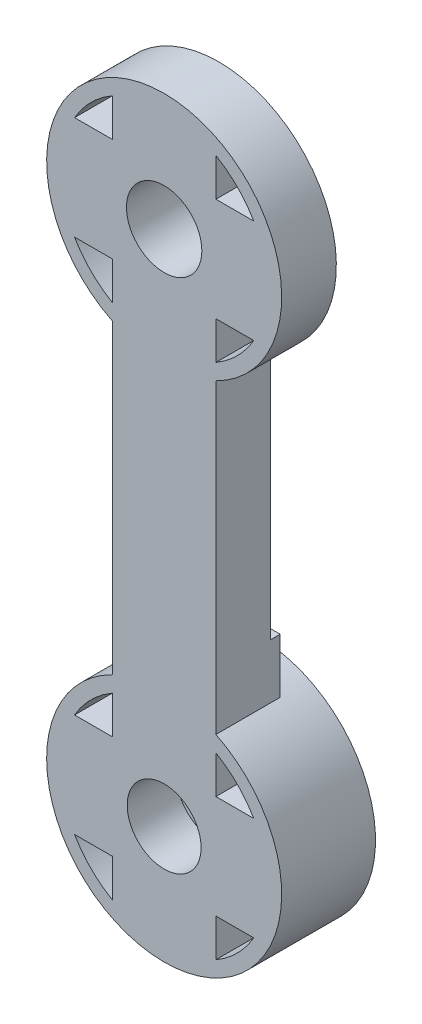
SolidWorks part; units mm, degrees
ref_plane "Front Plane" through (0, 0, 0) normal (0, 0, 1) x (1, 0, 0)
ref_plane "Top Plane" through (0, 0, 0) normal (0, 1, 0) x (1, 0, 0)
ref_plane "Right Plane" through (0, 0, 0) normal (1, 0, 0) x (0, 0, -1)
sketch "Sketch1" plane through (0, 0, 0) normal (0, 0, 1) x (1, 0, 0)
  line L5 (0, -17.5) -> (12.7696, -17.5) construction
  line L26 (0, 0) -> (0, -35) construction
  line L32 (0, 3.5) -> (7.1381, 3.5)
  line L33 (7.1381, 3.5) -> (-7.1381, 3.5)
  line L34 (0, -3.5) -> (7.1381, -3.5)
  line L35 (7.1381, -3.5) -> (-7.1381, -3.5)
  line L36 (3.5, -35) -> (3.5, -41.0622)
  line L37 (-3.5, -35) -> (-3.5, -41.0622)
  line L38 (-3.5, 0) -> (-3.5, 6.0622)
  line L45 (-3.5, 0) -> (-3.5, -35)
  line L47 (3.5, 0) -> (3.5, -35)
  line L48 (3.5, 0) -> (3.5, 6.0622)
  line L49 (7.1381, -31.5) -> (-7.1381, -31.5)
  line L50 (0, -31.5) -> (7.1381, -31.5)
  line L51 (7.1381, -38.5) -> (-7.1381, -38.5)
  line L52 (0, -38.5) -> (7.1381, -38.5)
  circle A0 centre (0, 0) radius 7.95
  circle A1 centre (0, 0) radius 3.5
  circle A2 centre (0, 0) radius 7
  circle A6 centre (0, 0) radius 1.5
  circle A11 centre (0, -35) radius 1.5
  circle A12 centre (0, -35) radius 7
  circle A13 centre (0, -35) radius 3.5
  circle A14 centre (0, -35) radius 7.95
  point P20 (0, -35)
  point P34 (0, -35)
  point P42 (0, 0)
  dimension "D1" = 15.9
  dimension "D2" = 7
  dimension "D6" = 14
  dimension "D9" = 3
  dimension "D3" = 7
  dimension "D7" = 35
extrude "Boss-Extrude4" add sketch "Sketch1" along normal blind 3 contours L48 A2 L38 L33 L32 | A2 L32 A0 L33 | L45 A14 L47 A0 | A14 L51 A12 | A12 L36 L51 L37 | A14 L49 A12 L51 | L36 A13 L51 | L51 A13 L37 | A14 L51 A12 L49 | A13 A11 | L45 A13 L49 | L49 A13 L47 | A12 L45 L49 L47 | A14 L49 A12 L45 | A14 L47 A12 L49 | A14 L45 A12 L47 | A12 L51 L37 L45 L49 | A12 L50 L47 L36 L52 | L45 A2 L47 L34 L35 | A2 L45 A0 L47 | A2 L47 A0 L34 | A2 L34 A0 L32 | A2 L33 A0 L35 | A2 L35 A0 L45 | L33 A2 L35 L45 L38 | L35 A2 L33 L48 L47 | A1 L34 L47 | A1 A6 | A1 L45 L35 | A1 L33 L38 | A1 L48 L32
sketch "Sketch3" plane through (0, 0, 0) normal (0, 0, -1) x (-1, 0, 0)
  line L0 (-3.5, 6.0622) -> (-3.5, 3.5)
  line L1 (-3.5, 3.5) -> (-6.0622, 3.5)
  line L2 (-3.5, -6.0622) -> (-3.5, -3.5)
  line L3 (-3.5, -3.5) -> (-6.0622, -3.5)
  line L4 (3.5, -6.0622) -> (3.5, -3.5)
  line L5 (3.5, -3.5) -> (6.0622, -3.5)
  line L6 (3.5, 6.0622) -> (3.5, 3.5)
  line L7 (3.5, 3.5) -> (6.0622, 3.5)
  line L8 (0, 0) -> (0, -35) construction
  line L9 (0, -35) -> (0, -17.5) construction
  line L10 (0, -17.5) -> (14.5774, -17.5) construction
  line L11 (-3.5, 3.5) -> (-6.0622, 3.5)
  line L12 (-3.5, 6.0622) -> (-3.5, 3.5)
  line L13 (-3.5, -3.5) -> (-6.0622, -3.5)
  line L14 (-3.5, -6.0622) -> (-3.5, -3.5)
  line L15 (3.5, -3.5) -> (6.0622, -3.5)
  line L16 (3.5, -6.0622) -> (3.5, -3.5)
  line L17 (3.5, 3.5) -> (6.0622, 3.5)
  line L18 (3.5, 6.0622) -> (3.5, 3.5)
  line L19 (3.5, -41.0622) -> (3.5, -38.5)
  line L20 (3.5, -38.5) -> (6.0622, -38.5)
  line L21 (3.5, -28.9378) -> (3.5, -31.5)
  line L22 (3.5, -31.5) -> (6.0622, -31.5)
  line L23 (-3.5, -28.9378) -> (-3.5, -31.5)
  line L24 (-3.5, -31.5) -> (-6.0622, -31.5)
  line L25 (-3.5, -41.0622) -> (-3.5, -38.5)
  line L26 (-3.5, -38.5) -> (-6.0622, -38.5)
  line L27 (3.5, -38.5) -> (6.0622, -38.5)
  line L28 (3.5, -41.0622) -> (3.5, -38.5)
  line L29 (3.5, -31.5) -> (6.0622, -31.5)
  line L30 (3.5, -28.9378) -> (3.5, -31.5)
  line L31 (-3.5, -31.5) -> (-6.0622, -31.5)
  line L32 (-3.5, -28.9378) -> (-3.5, -31.5)
  line L33 (-3.5, -38.5) -> (-6.0622, -38.5)
  line L34 (-3.5, -41.0622) -> (-3.5, -38.5)
  circle A0 centre (0, 0) radius 1.5
  circle A1 centre (0, 0) radius 7.95
  circle A2 centre (0, 0) radius 7
  circle A3 centre (0, -35) radius 7
  circle A4 centre (0, -35) radius 7.95
  circle A5 centre (0, -35) radius 1.5
  line M2 (3.5, -38.5) -> (6.0622, -38.5)
  arc M3 (6.0622, -38.5) -> (3.5, -41.0622) centre (0, -35) cw
  line M4 (3.5, -41.0622) -> (3.5, -38.5)
  line M5 (-3.5, -38.5) -> (-3.5, -41.0622)
  arc M6 (-3.5, -41.0622) -> (-6.0622, -38.5) centre (0, -35) cw
  line M7 (-6.0622, -38.5) -> (-3.5, -38.5)
  arc M9 (3.5, -7.1381) -> (-3.5, -7.1381) centre (0, 0) ccw
  arc M11 (-3.5, -27.8619) -> (3.5, -27.8619) centre (0, -35) ccw
  line M12 (6.0622, -31.5) -> (3.5, -31.5)
  line M13 (3.5, -31.5) -> (3.5, -28.9378)
  arc M14 (3.5, -28.9378) -> (6.0622, -31.5) centre (0, -35) cw
  arc M15 (-3.5, -6.0622) -> (-6.0622, -3.5) centre (0, 0) cw
  line M16 (-6.0622, -3.5) -> (-3.5, -3.5)
  line M17 (-3.5, -3.5) -> (-3.5, -6.0622)
  line M18 (-3.5, -31.5) -> (-6.0622, -31.5)
  arc M19 (-6.0622, -31.5) -> (-3.5, -28.9378) centre (0, -35) cw
  line M20 (-3.5, -28.9378) -> (-3.5, -31.5)
  line M21 (3.5, -3.5) -> (6.0622, -3.5)
  arc M22 (6.0622, -3.5) -> (3.5, -6.0622) centre (0, 0) cw
  line M23 (3.5, -6.0622) -> (3.5, -3.5)
  line M24 (6.0622, 3.5) -> (3.5, 3.5)
  line M25 (3.5, 3.5) -> (3.5, 6.0622)
  arc M26 (3.5, 6.0622) -> (6.0622, 3.5) centre (0, 0) cw
  arc M27 (-6.0622, 3.5) -> (-3.5, 6.0622) centre (0, 0) cw
  line M28 (-3.5, 6.0622) -> (-3.5, 3.5)
  line M29 (-3.5, 3.5) -> (-6.0622, 3.5)
  circle M30 centre (0, 0) radius 1.5
  circle M31 centre (0, -35) radius 1.5
  dimension "D1" = 15.9
extrude "Boss-Extrude5" add sketch "Sketch3" along normal blind 3 contours A1 A2 M9 M26 M22 M15 M27 | A2 M25 M28 M29 M16 M17 M23 M21 M24 M30 | A3 M4 M2 M12 M13 M20 M18 M7 M5 M31 | A4 A3 M11 M3 M6 M19 M14
sketch "Sketch4" plane through (0, 0, 3) normal (0, 0, 1) x (1, 0, 0)
  line L0 (0, 0) -> (0, -35) construction
  line L1 (0, -35) -> (0, 0) construction
  line L2 (0, -17.5) -> (19.6941, -17.5) construction
  circle A1 centre (0, -35) radius 2.5
  circle A2 centre (0, 0) radius 2.5
  dimension "D2" = 5
extrude "Cut-Extrude1" cut sketch "Sketch4" against normal blind 1.5
sketch "Sketch5" plane through (0, 0, -3) normal (0, 0, -1) x (-1, 0, 0)
  circle A0 centre (0, 0) radius 7
extrude "Cut-Extrude2" cut sketch "Sketch5" against normal blind 2
sketch "Sketch6" plane through (0, 0, -3) normal (0, 0, -1) x (-1, 0, 0)
  circle A0 centre (0, -35) radius 7.95
extrude "Cut-Extrude3" cut sketch "Sketch6" against normal blind 1
sketch "Sketch7" plane through (0, 0, 1.5) normal (0, 0, 1) x (1, 0, 0)
  circle A0 centre (0, -35) radius 2.5
extrude "Cut-Extrude4" cut sketch "Sketch7" against normal blind 1.85
sketch "Sketch8" plane through (0, 0, -3) normal (0, 0, -1) x (-1, 0, 0)
  circle A0 centre (0, 0) radius 7.95
  circle A1 centre (0, 0) radius 7
extrude "Boss-Extrude6" add sketch "Sketch8" along normal blind 0.7
sketch "Sketch9" plane through (0, 0, -2) normal (0, 0, -1) x (-1, 0, 0)
  line L0 (-3.5, -28.9378) -> (-3.5, -31.5)
  line L1 (-3.5, -31.5) -> (-6.0622, -31.5)
  line L2 (-6.0622, -38.5) -> (-3.5, -38.5)
  line L3 (-3.5, -38.5) -> (-3.5, -41.0622)
  line L4 (6.0622, -38.5) -> (3.5, -38.5)
  line L5 (3.5, -38.5) -> (3.5, -41.0622)
  line L6 (3.5, -28.9378) -> (3.5, -31.5)
  line L7 (3.5, -31.5) -> (6.0622, -31.5)
  circle A0 centre (0, -35) radius 7.95
  circle A1 centre (0, -35) radius 7
  circle A2 centre (0, -35) radius 1.5
  line M1 (6.0622, -31.5) -> (3.5, -31.5)
  line M2 (3.5, -31.5) -> (3.5, -28.9378)
  arc M3 (3.5, -28.9378) -> (6.0622, -31.5) centre (0, -35) cw
  arc M4 (-3.5, -41.0622) -> (-6.0622, -38.5) centre (0, -35) cw
  line M5 (-6.0622, -38.5) -> (-3.5, -38.5)
  line M6 (-3.5, -38.5) -> (-3.5, -41.0622)
  arc M7 (6.0622, -38.5) -> (3.5, -41.0622) centre (0, -35) cw
  line M8 (3.5, -41.0622) -> (3.5, -38.5)
  line M9 (3.5, -38.5) -> (6.0622, -38.5)
  circle M10 centre (0, -35) radius 7.95
  line M11 (-3.5, -31.5) -> (-6.0622, -31.5)
  arc M12 (-6.0622, -31.5) -> (-3.5, -28.9378) centre (0, -35) cw
  line M13 (-3.5, -28.9378) -> (-3.5, -31.5)
  circle M14 centre (0, -35) radius 1.5
extrude "Boss-Extrude8" add sketch "Sketch9" along normal blind 0.7 contours A1 M2 M13 M11 M5 M6 M8 M9 M1 M14 | A1 M10 M3 M7 M4 M12 | A0
sketch "Sketch10" plane through (0, 0, 0) normal (0, 0, -1) x (-1, 0, 0)
  line L2 (-3.5, -7.1381) -> (-3.5, -27.8619)
  line L4 (3.5, -7.1381) -> (3.5, -27.8619)
  circle A0 centre (0, 0) radius 7.95
  circle A1 centre (0, -35) radius 7.95
  line M1 (-3.5, -7.1381) -> (-3.5, -27.8619)
  arc M2 (-3.5, -27.8619) -> (3.5, -27.8619) centre (0, -35) cw
  line M3 (3.5, -27.8619) -> (3.5, -7.1381)
  arc M4 (3.5, -7.1381) -> (-3.5, -7.1381) centre (0, 0) cw
extrude "Boss-Extrude9" add sketch "Sketch10" along normal blind 0.7 contours M4 M1 M2 M3
sketch "Sketch11" plane through (3.5, 0, 0) normal (1, 0, 0) x (0, 0, -1)
  line L0 (-3, -42.95) -> (2.7, -42.95) construction
  line L1 (3.7, 7.95) -> (0.7, 7.95)
  line L2 (3.7, 7.95) -> (3.7, -7.95)
  line L3 (3.7, -7.95) -> (0.7, -7.95)
  line L4 (0.7, 7.95) -> (0.7, -7.95)
  line L5 (2.7, -27.05) -> (0.7, -27.05)
  line L6 (2.7, -27.05) -> (2.7, -42.95)
  line L7 (2.7, -42.95) -> (0.7, -42.95)
  line L8 (0.7, -27.05) -> (0.7, -42.95)
extrude "Cut-Extrude5" cut sketch "Sketch11" against normal through all both and the other way through all
sketch "Sketch12" plane through (0, 0, -0.7) normal (0, 0, -1) x (-1, 0, 0)
  line L0 (3.5, -27.8619) -> (3.5, -7.1381) construction
  line L1 (-3.5, -27.8619) -> (3.5, -27.8619)
  line L2 (-3.5, -27.8619) -> (-3.5, -24.1619)
  line L3 (-3.5, -24.1619) -> (3.5, -24.1619)
  line L4 (3.5, -27.8619) -> (3.5, -24.1619)
  circle A0 centre (0, -35) radius 7.95
  line M3 (3.5, -27.8619) -> (3.5, -7.1381)
  line M5 (-3.5, -7.1381) -> (-3.5, -27.8619)
  dimension "D1" = 3.7
extrude "Boss-Extrude10" add sketch "Sketch12" along normal blind 0.65 contours A0 L3 M3 M5
sketch "Sketch13" plane through (0, 0, -0.7) normal (0, 0, -1) x (-1, 0, 0)
  line L0 (-6.0622, -31.5) -> (-3.5, -31.5)
  line L1 (-3.5, -31.5) -> (-3.5, -28.9378)
  line L2 (3.5, -28.9378) -> (3.5, -31.5)
  line L3 (3.5, -31.5) -> (6.0622, -31.5)
  line L4 (-6.0622, -38.5) -> (-3.5, -38.5)
  line L5 (-3.5, -38.5) -> (-3.5, -41.0622)
  line L6 (6.0622, -38.5) -> (3.5, -38.5)
  line L7 (3.5, -38.5) -> (3.5, -41.0622)
  circle A0 centre (0, -35) radius 1.5
  circle A1 centre (0, -35) radius 7.95
  circle A2 centre (0, -35) radius 7
  arc M1 (-6.0622, -31.5) -> (-3.5, -28.9378) centre (0, -35) cw
  line M2 (-3.5, -28.9378) -> (-3.5, -31.5)
  line M3 (-3.5, -31.5) -> (-6.0622, -31.5)
  line M4 (3.5, -31.5) -> (3.5, -28.9378)
  arc M5 (3.5, -28.9378) -> (6.0622, -31.5) centre (0, -35) cw
  line M6 (6.0622, -31.5) -> (3.5, -31.5)
  line M7 (3.5, -38.5) -> (6.0622, -38.5)
  arc M8 (6.0622, -38.5) -> (3.5, -41.0622) centre (0, -35) cw
  line M9 (3.5, -41.0622) -> (3.5, -38.5)
  line M10 (-3.5, -38.5) -> (-3.5, -41.0622)
  arc M11 (-3.5, -41.0622) -> (-6.0622, -38.5) centre (0, -35) cw
  line M12 (-6.0622, -38.5) -> (-3.5, -38.5)
  circle M13 centre (0, -35) radius 1.5
  arc M14 (-3.5, -27.8619) -> (3.5, -27.8619) centre (0, -35) ccw
  arc M15 (3.5, -27.8619) -> (-3.5, -27.8619) centre (0, -35) ccw
extrude "Boss-Extrude11" add sketch "Sketch13" along normal blind 2.65 contours A2 M15 M14 M5 M8 M11 M1 | A2 M4 M2 M3 M12 M10 M9 M7 M6 M13
sketch "Sketch14" plane through (0, 0, 3) normal (0, 0, 1) x (1, 0, 0)
  circle A0 centre (0, 0) radius 2.55
  dimension "D1" = 5.1
extrude "Cut-Extrude6" cut sketch "Sketch14" against normal through all
